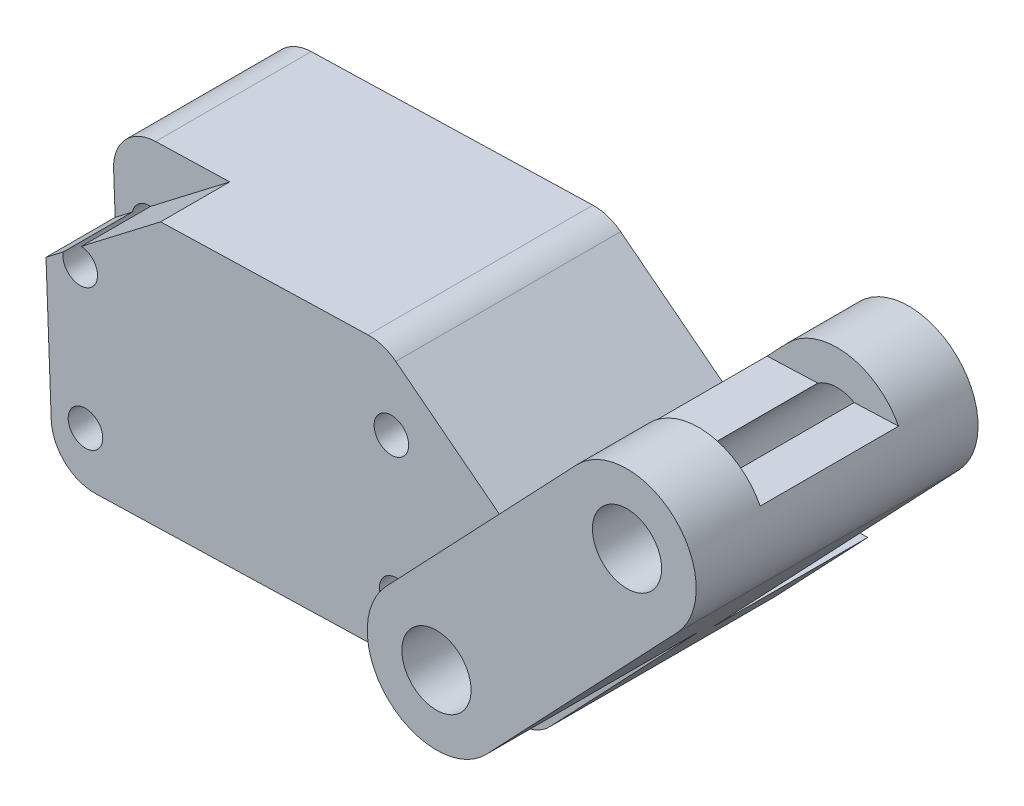
SolidWorks part; units mm, degrees
ref_plane "Front Plane" through (0, 0, 0) normal (0, 0, 1) x (1, 0, 0)
ref_plane "Top Plane" through (0, 0, 0) normal (0, 1, 0) x (1, 0, 0)
ref_plane "Right Plane" through (0, 0, 0) normal (1, 0, 0) x (0, 0, -1)
sketch "Sketch1" plane through (0, 0, 0) normal (0, 0, 1) x (1, 0, 0)
  line L0 (32.3642, 102.0094) -> (99.3483, 100.5495) construction
  line L1 (75.3027, 213.5128) -> (47.9556, 184.735) construction
  line L2 (37.4462, 199.1002) -> (21.1579, 198.6451)
  line L3 (18.7295, 196.0515) -> (19.1221, 185.6774)
  line L4 (21.6902, 183.2729) -> (46.2132, 183.9581)
  line L5 (47.9556, 184.735) -> (53.3406, 190.4018)
  line L6 (53.3406, 190.4018) -> (50.4213, 190.4018)
  line L7 (48.8869, 190.928) -> (39.0504, 198.5749)
  line L8 (13.2611, 186.0386) -> (61.3099, 187.3811) construction
  line L9 (20.5264, 201.4562) -> (21.4326, 177.511) construction
  line L10 (38.5155, 202.0855) -> (39.4957, 176.1853) construction
  line L11 (16.2054, 194.1239) -> (57.682, 195.2828) construction
  arc A0 (37.4462, 199.1002) -> (39.0504, 198.5749) centre (37.516, 196.6012) cw
  arc A1 (48.8869, 190.928) -> (50.4213, 190.4018) centre (50.4213, 192.9018) ccw
  arc A2 (47.9556, 184.735) -> (46.2132, 183.9581) centre (46.1433, 186.4571) cw
  arc A3 (21.6902, 183.2729) -> (19.1221, 185.6774) centre (21.6203, 185.7719) cw
  arc A4 (18.7295, 196.0515) -> (21.1579, 198.6451) centre (21.2277, 196.146) cw
  circle A5 centre (20.799, 194.2523) radius 1
  circle A6 centre (38.7929, 194.7551) radius 1
  circle A7 centre (39.0955, 186.7604) radius 1
  circle A8 centre (21.1016, 186.2576) radius 1
  dimension "D2" = 48.0489
  dimension "D7" = 2
  dimension "D8" = 2
  dimension "D9" = 2
  dimension "D10" = 2
  dimension "D1" = 67
  dimension "D3" = 3
  dimension "D4" = 2
  dimension "D5" = 18
  dimension "D6" = 8
extrude "Boss-Extrude1" add sketch "Sketch1" along normal blind 9
sketch "Sketch2" plane through (0, 0, 9) normal (0, 0, 1) x (1, 0, 0)
  line L0 (25.4462, 198.7649) -> (18.8194, 193.6774)
  line L1 (37.4462, 199.1002) -> (21.1579, 198.6451) construction
  line L2 (18.7295, 196.0515) -> (19.1221, 185.6774) construction
  line L3 (18.8194, 193.6774) -> (19.1221, 185.6774)
  line L4 (21.6902, 183.2729) -> (46.2132, 183.9581)
  line L5 (47.9556, 184.735) -> (67.6197, 205.4278)
  line L6 (61.8205, 210.9387) -> (45.3889, 193.6474)
  line L7 (61.8205, 210.9387) -> (67.6197, 205.4278) construction
  line L8 (48.8869, 190.928) -> (39.0504, 198.5749) construction
  line L9 (45.3889, 193.6474) -> (39.0504, 198.5749)
  line L10 (45.3889, 193.6474) -> (35.9076, 183.6701) construction
  line L11 (37.4462, 199.1002) -> (25.4462, 198.7649)
  line L12 (21.6902, 183.2729) -> (46.2132, 183.9581) construction
  line L13 (64.7201, 208.1832) -> (53.6984, 196.5849) construction
  line L14 (21.1016, 186.2576) -> (39.0955, 186.7604) construction
  line L15 (39.0955, 186.7604) -> (50.1745, 187.0699) construction
  line L16 (47.9556, 184.735) -> (53.3406, 190.4018) construction
  line L17 (64.7201, 208.1832) -> (53.6984, 196.5849) construction
  line L18 (53.6984, 196.5849) -> (44.5059, 186.9116) construction
  arc A0 (46.2132, 183.9581) -> (47.9556, 184.735) centre (46.1433, 186.4571) ccw
  arc A1 (61.8205, 210.9387) -> (67.6197, 205.4278) centre (64.7201, 208.1832) cw
  circle A2 centre (64.7201, 208.1832) radius 2
  arc A3 (39.0504, 198.5749) -> (37.4462, 199.1002) centre (37.516, 196.6012) ccw construction
  arc A4 (37.4462, 199.1002) -> (39.0504, 198.5749) centre (37.516, 196.6012) cw
  arc A5 (19.1221, 185.6774) -> (21.6902, 183.2729) centre (21.6203, 185.7719) ccw
  circle A6 centre (53.6984, 196.5849) radius 2
  arc M6 (39.0504, 198.5749) -> (37.4462, 199.1002) centre (37.516, 196.6012) ccw
  line M7 (37.4462, 199.1002) -> (21.1579, 198.6451)
  line M9 (18.7295, 196.0515) -> (19.1221, 185.6774)
  arc M10 (19.1221, 185.6774) -> (21.6902, 183.2729) centre (21.6203, 185.7719) ccw
  line M11 (21.6902, 183.2729) -> (46.2132, 183.9581)
  arc M12 (46.2132, 183.9581) -> (47.9556, 184.735) centre (46.1433, 186.4571) ccw
  line M13 (47.9556, 184.735) -> (53.3406, 190.4018)
  line M14 (53.3406, 190.4018) -> (50.4213, 190.4018)
  arc M15 (50.4213, 190.4018) -> (48.8869, 190.928) centre (50.4213, 192.9018) cw
  line M16 (48.8869, 190.928) -> (39.0504, 198.5749)
  circle M17 centre (20.799, 194.2523) radius 1
  circle M18 centre (38.7929, 194.7551) radius 1
  circle M19 centre (39.0955, 186.7604) radius 1
  circle M20 centre (21.1016, 186.2576) radius 1
  dimension "D5" = 4
  dimension "D6" = 4
  dimension "D1" = 8
  dimension "D2" = 12
  dimension "D3" = 8
  dimension "D4" = 33.4
  dimension "D7" = 16
extrude "Boss-Extrude3" add sketch "Sketch2" along normal blind 4 contours A1 L6 L5 A6 A2 M16 M15 M14 | L0 M7 M17 M9 M10 M11 M12 M13 M14 M15 M16 M6 M19 M20 M18
sketch "Sketch3" plane through (0, 0, 13) normal (0, 0, 1) x (1, 0, 0)
  line L0 (64.7201, 208.1832) -> (53.6984, 196.5849) construction
  line L1 (64.7201, 208.1832) -> (53.6984, 196.5849) construction
  line L2 (67.6197, 205.4278) -> (56.5979, 193.8295)
  line L3 (61.8205, 210.9387) -> (50.7988, 199.3403)
  arc A0 (67.6197, 205.4278) -> (61.8205, 210.9387) centre (64.7201, 208.1832) ccw
  arc A1 (50.7988, 199.3403) -> (56.5979, 193.8295) centre (53.6984, 196.5849) ccw
  arc A2 (67.6197, 205.4278) -> (61.8205, 210.9387) centre (64.7201, 208.1832) ccw construction
  circle A3 centre (64.7201, 208.1832) radius 2
  circle A4 centre (53.6984, 196.5849) radius 2
  point P4 (59.2092, 202.3841)
extrude "Boss-Extrude4" add sketch "Sketch3" along normal blind 12.3
sketch "Sketch4" plane through (26.1116, 0.9882, 0) normal (-0.9993, -0.0378, 0) x (0, 0, 1)
  line L0 (13.15, 209.5868) -> (13.15, 207.2868)
  line L2 (13.15, 207.2868) -> (21.15, 207.2868)
  line L3 (21.15, 207.2868) -> (21.15, 209.5868)
  line L4 (21.15, 209.5868) -> (13.15, 209.5868)
  line L5 (9, 209.5868) -> (25.3, 209.5868) construction
  point P2 (17.15, 209.5868)
  point P3 (17.15, 209.5868)
  dimension "D1" = 8
  dimension "D2" = 2.3
extrude "Cut-Extrude1" cut sketch "Sketch4" against normal blind 100
ref_plane "Plane1" through (0, 0, 17.15) normal (0, 0, 1) x (1, 0, 0)
